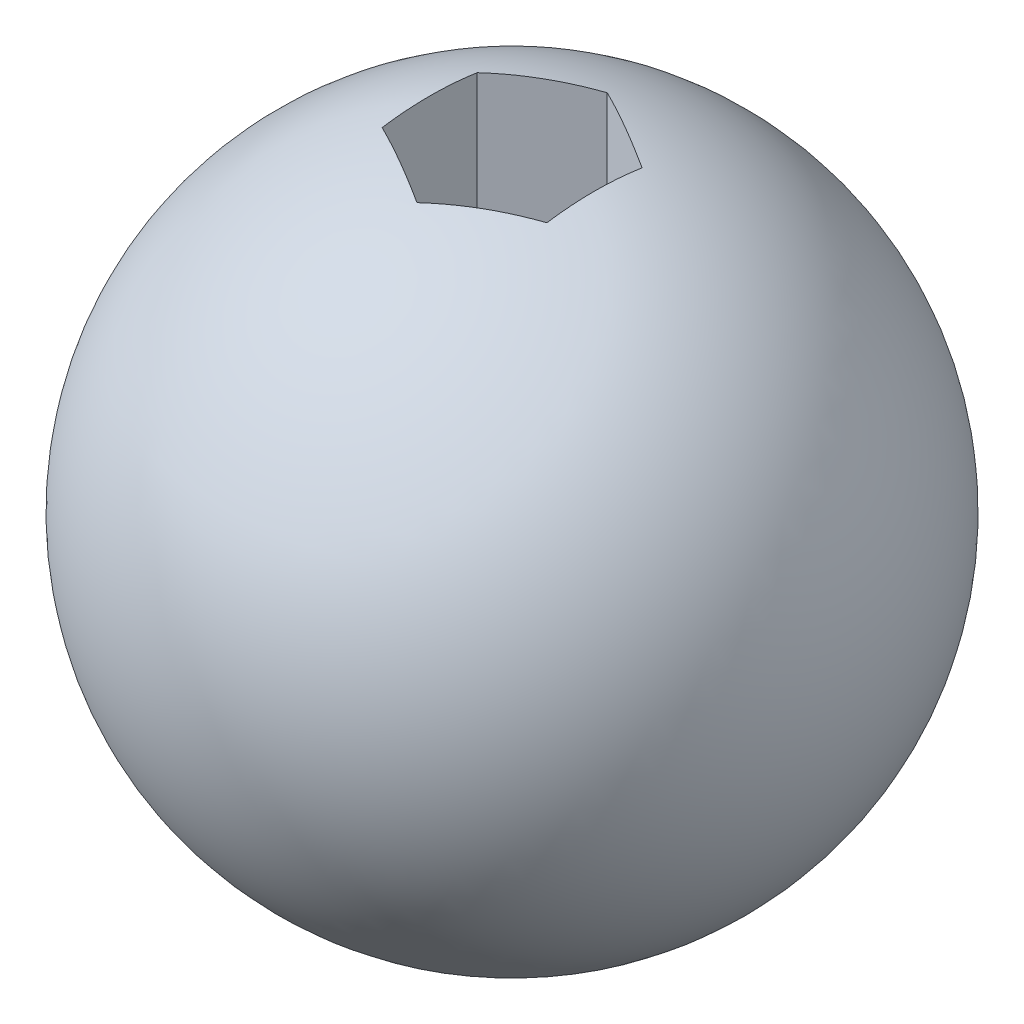
SolidWorks part; units mm, degrees
ref_plane "Plan de face" through (0, 0, 0) normal (0, 0, 1) x (1, 0, 0)
ref_plane "Plan de dessus" through (0, 0, 0) normal (0, 1, 0) x (1, 0, 0)
ref_plane "Plan de droite" through (0, 0, 0) normal (1, 0, 0) x (0, 0, -1)
sketch "Esquisse1" plane through (0, 0, 0) normal (0, 0, 1) x (1, 0, 0)
  line L0 (0, 38.8304) -> (0, -36.4578) construction
  line L1 (0, 20) -> (0, -20)
  arc A0 (0, 20) -> (0, -20) centre (0, 0) cw
  dimension "D1" = 20
revolve "Révolution1" add sketch "Esquisse1" angle 360 about L0
sketch "Esquisse2" plane through (0, 0, 0) normal (0, 1, 0) x (1, 0, 0)
  line L1 (5, -2.8868) -> (5, 2.8868)
  line L2 (5, 2.8868) -> (0, 5.7735)
  line L3 (0, 5.7735) -> (-5, 2.8868)
  line L4 (-5, 2.8868) -> (-5, -2.8868)
  line L5 (-5, -2.8868) -> (0, -5.7735)
  line L6 (0, -5.7735) -> (5, -2.8868)
  circle A0 centre (0, 0) radius 5 construction
  dimension "D1" = 10
extrude "Enlèv. mat.-Extru.1" cut sketch "Esquisse2" along normal through all
sketch "Esquisse3" plane through (0, 0, 0) normal (0, 1, 0) x (1, 0, 0)
  circle A0 centre (0, 0) radius 3
  dimension "D1" = 6
extrude "Enlèv. mat.-Extru.2" cut sketch "Esquisse3" against normal through all
sketch "Esquisse5" plane through (0, 0, 0) normal (0, 0, 1) x (1, 0, 0)
  line L0 (31.7269, -16) -> (-44.0249, -16)
  dimension "D1" = 16
extrude "Enlèv. mat.-Extru.3" cut sketch "Esquisse5" against normal through all and the other way through all
